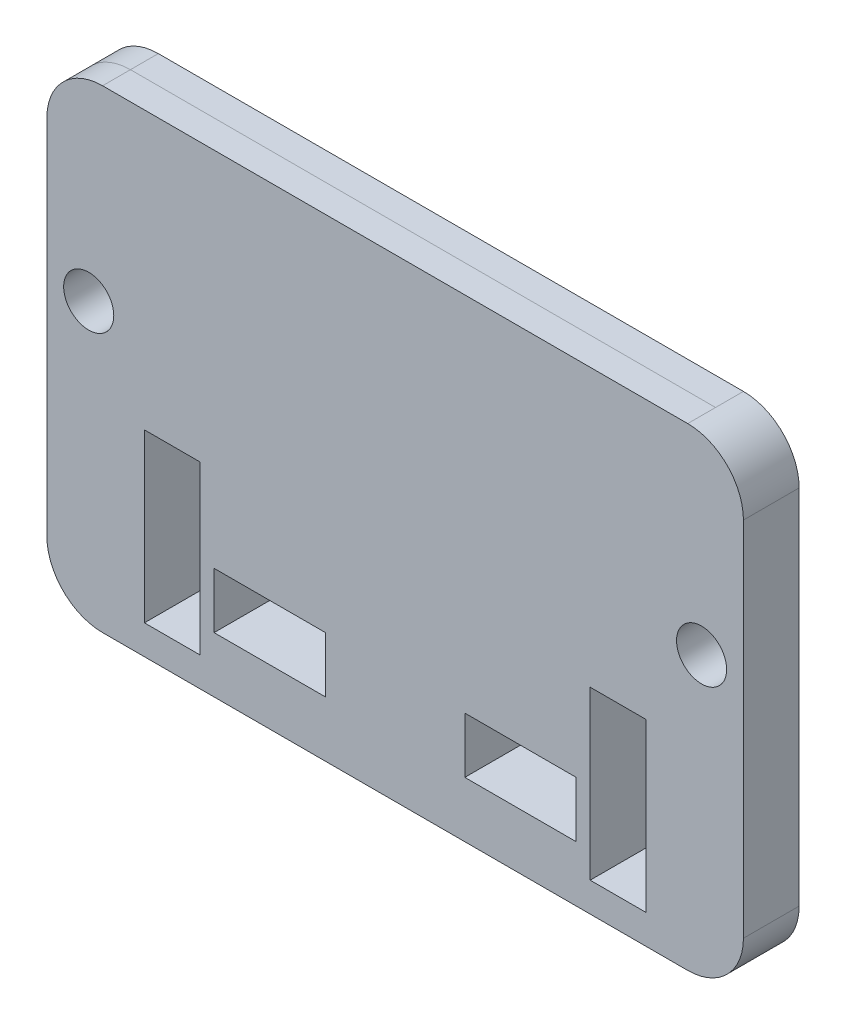
SolidWorks part; units mm, degrees
material "Pink Foam"
ref_plane "Front Plane" through (0, 0, 0) normal (0, 0, 1) x (1, 0, 0)
ref_plane "Top Plane" through (0, 0, 0) normal (0, 1, 0) x (1, 0, 0)
ref_plane "Right Plane" through (0, 0, 0) normal (1, 0, 0) x (0, 0, -1)
sketch "Sketch1" plane through (0, 0, 0) normal (0, 0, 1) x (1, 0, 0)
  line L1 (-139.7, -203.2) -> (139.7, -203.2) construction
  line L2 (-165.1, -177.8) -> (-165.1, 177.8) construction
  line L3 (-139.7, 203.2) -> (139.7, 203.2) construction
  line L4 (165.1, -177.8) -> (165.1, 177.8) construction
  line L5 (-165.1, -203.2) -> (165.1, 203.2) construction
  line L6 (-165.1, 203.2) -> (165.1, -203.2) construction
  line L7 (-133.3733, -107.95) -> (133.3733, -107.95)
  line L8 (-158.7733, -82.55) -> (-158.7733, 82.55)
  line L9 (-133.3733, 107.95) -> (133.3733, 107.95)
  line L10 (158.7733, -82.55) -> (158.7733, 82.55)
  line L11 (-158.7733, -107.95) -> (158.7733, 107.95) construction
  line L12 (-158.7733, 107.95) -> (158.7733, -107.95) construction
  arc A0 (-139.7, -203.2) -> (-165.1, -177.8) centre (-139.7, -177.8) cw construction
  arc A1 (139.7, -203.2) -> (165.1, -177.8) centre (139.7, -177.8) ccw construction
  arc A2 (139.7, 203.2) -> (165.1, 177.8) centre (139.7, 177.8) cw construction
  arc A3 (-165.1, 177.8) -> (-139.7, 203.2) centre (-139.7, 177.8) cw construction
  circle A4 centre (-139.7, 19.7399) radius 11.422
  circle A5 centre (139.7, 19.7399) radius 11.422
  arc A6 (-133.3733, -107.95) -> (-158.7733, -82.55) centre (-133.3733, -82.55) cw
  arc A7 (133.3733, -107.95) -> (158.7733, -82.55) centre (133.3733, -82.55) ccw
  arc A8 (133.3733, 107.95) -> (158.7733, 82.55) centre (133.3733, 82.55) cw
  arc A9 (-158.7733, 82.55) -> (-133.3733, 107.95) centre (-133.3733, 82.55) cw
  point P0 (0, 0)
  point P23 (0, 0)
  dimension "D3" = 25.4
  dimension "D7" = 22.844
  dimension "D8" = 317.5465
  dimension "D10" = 25.4
  dimension "D1" = 330.2
  dimension "D2" = 406.4
  dimension "D4" = 25.4
  dimension "D5" = 88.2101
  dimension "D6" = 25.4
  dimension "D9" = 215.9
extrude "Boss-Extrude1" add sketch "Sketch1" along normal blind 25.4
ref_plane "Plane1" through (0, 0, 12.7) normal (0, 0, 1) x (1, 0, 0)
sketch "Sketch2" plane through (0, 0, 0) normal (0, 0, -1) x (-1, 0, 0)
  line L0 (0, 0) -> (0, -69.85) construction
  line L2 (-114.3, -69.85) -> (0, -69.85) construction
  line L3 (0, -69.85) -> (114.3, -69.85) construction
  line L4 (-82.55, -82.55) -> (-31.75, -82.55)
  line L5 (-82.55, -82.55) -> (-82.55, -57.15)
  line L6 (-82.55, -57.15) -> (-31.75, -57.15)
  line L7 (-31.75, -82.55) -> (-31.75, -57.15)
  line L8 (-82.55, -82.55) -> (-31.75, -57.15) construction
  line L9 (-82.55, -57.15) -> (-31.75, -82.55) construction
  line L10 (31.75, -82.55) -> (82.55, -82.55)
  line L11 (31.75, -82.55) -> (31.75, -57.15)
  line L12 (31.75, -57.15) -> (82.55, -57.15)
  line L13 (82.55, -82.55) -> (82.55, -57.15)
  line L14 (31.75, -82.55) -> (82.55, -57.15) construction
  line L15 (31.75, -57.15) -> (82.55, -82.55) construction
  point P5 (-57.15, -69.85)
  point P6 (57.15, -69.85)
  point P7 (-57.15, -69.85)
  point P12 (57.15, -69.85)
  dimension "D1" = 228.6
  dimension "D2" = 69.85
  dimension "D3" = 25.4
  dimension "D4" = 50.8
  dimension "D5" = 50.8
  dimension "D6" = 25.4
extrude "Foam Insert Cut-Throughs" cut sketch "Sketch2" against normal blind 25.4
split line "Split Line1"
sketch "Sketch3" plane through (0, 0, 0) normal (0, 0, -1) x (-1, 0, 0)
  line L24 (88.9, -94.5601) -> (88.9, -18.3601)
  line L25 (88.9, -18.3601) -> (114.3, -18.3601)
  line L26 (114.3, -18.3601) -> (114.3, -94.5601)
  line L27 (114.3, -94.5601) -> (88.9, -94.5601)
  line L28 (-114.3, -94.5601) -> (-114.3, -18.3601)
  line L29 (-114.3, -18.3601) -> (-88.9, -18.3601)
  line L30 (-88.9, -18.3601) -> (-88.9, -94.5601)
  line L31 (-88.9, -94.5601) -> (-114.3, -94.5601)
extrude "Cut-Extrude1" cut sketch "Sketch3" against normal blind 25.4
